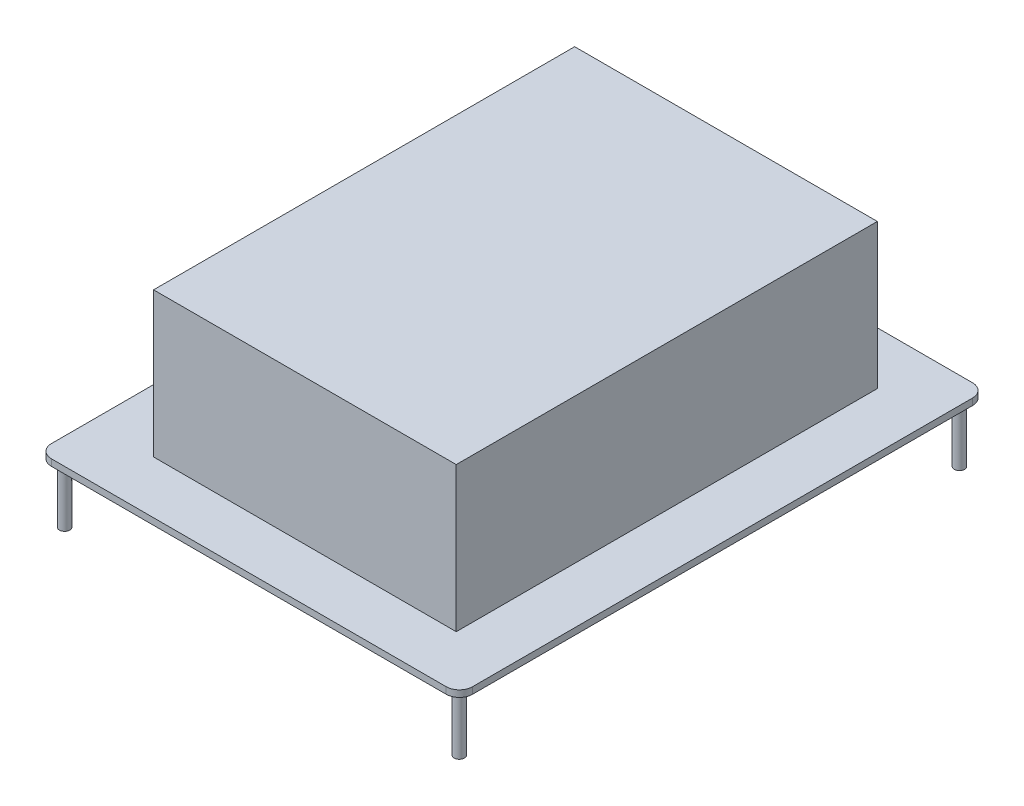
SolidWorks part; units mm, degrees
ref_plane "Front Plane" through (0, 0, 0) normal (0, 0, 1) x (1, 0, 0)
ref_plane "Top Plane" through (0, 0, 0) normal (0, 1, 0) x (1, 0, 0)
ref_plane "Right Plane" through (0, 0, 0) normal (1, 0, 0) x (0, 0, -1)
sketch "Sketch1" plane through (0, 0, 0) normal (0, 1, 0) x (1, 0, 0)
  line L1 (-40.64, -50.8) -> (40.64, -50.8)
  line L2 (-40.64, -50.8) -> (-40.64, 50.8)
  line L3 (-40.64, 50.8) -> (40.64, 50.8)
  line L4 (40.64, -50.8) -> (40.64, 50.8)
  line L5 (-40.64, -50.8) -> (40.64, 50.8) construction
  line L6 (-40.64, 50.8) -> (40.64, -50.8) construction
  point P0 (0, 0)
  dimension "D1" = 101.6
  dimension "D2" = 81.28
extrude "Boss-Extrude1" add sketch "Sketch1" along normal blind 1.27
sketch "Sketch2" plane through (0, 1.27, 0) normal (0, 1, 0) x (1, 0, 0)
  line L0 (-40.64, 0) -> (-16.4457, 0) construction
  line L1 (-28.5429, 40.64) -> (29.8771, 40.64)
  line L2 (-28.5429, 40.64) -> (-28.5429, -40.64)
  line L3 (-28.5429, -40.64) -> (29.8771, -40.64)
  line L4 (29.8771, 40.64) -> (29.8771, -40.64)
  line L5 (-40.64, 50.8) -> (-40.64, -50.8) construction
  point P9 (-28.5429, 0)
  dimension "D1" = 81.28
  dimension "D2" = 58.42
extrude "Boss-Extrude2" add sketch "Sketch2" along normal blind 27.94
fillet "Fillet1" radius 2.54 4 edges at (-40.64, 0.635, -50.8) (40.64, 0.635, -50.8) (40.64, 0.635, 50.8) (-40.64, 0.635, 50.8)
sketch "Sketch4" plane through (0, 0, 0) normal (0, -1, 0) x (1, 0, 0)
  line L0 (40.64, 0) -> (-57.2413, 0) construction
  line L2 (-38.1, 50.8) -> (38.1, 50.8) construction
  line L3 (0, 50.8) -> (0, -123.3424) construction
  line L4 (40.64, 48.26) -> (40.64, -48.26) construction
  circle A0 centre (38.1, 48.26) radius 1
  circle A2 centre (38.1, -48.26) radius 1
  circle A3 centre (-38.1, 48.26) radius 1
  circle A4 centre (-38.1, -48.26) radius 1
  dimension "D1" = 2
extrude "Boss-Extrude3" add sketch "Sketch4" along normal blind 11.43
